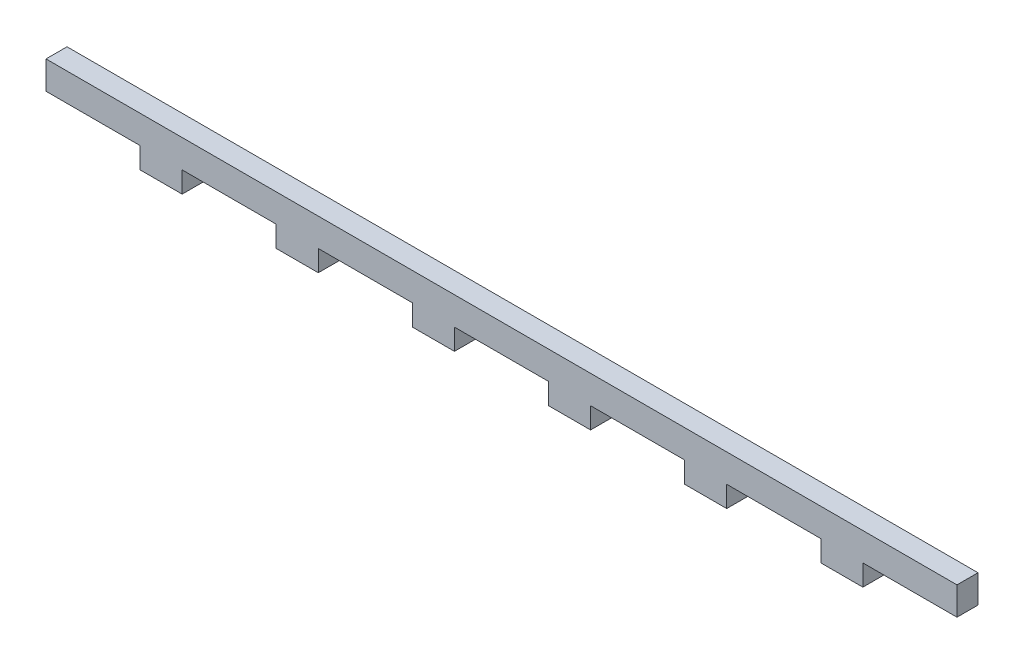
SolidWorks part; units mm, degrees
ref_plane "Front Plane" through (0, 0, 0) normal (0, 0, 1) x (1, 0, 0)
ref_plane "Top Plane" through (0, 0, 0) normal (0, 1, 0) x (1, 0, 0)
ref_plane "Right Plane" through (0, 0, 0) normal (1, 0, 0) x (0, 0, -1)
sketch "Sketch2" plane through (0, 0, 0) normal (0, 1, 0) x (1, 0, 0)
  line L0 (0, 0) -> (0, 6) construction
  dimension "D1" = 6
sketch "Sketch1" plane through (0, 0, 0) normal (0, 0, 1) x (1, 0, 0)
  line L1 (-130, -7) -> (130, -7)
  line L2 (-130, -7) -> (-130, 7)
  line L3 (-130, 7) -> (130, 7)
  line L4 (130, -7) -> (130, 7)
  line L5 (-130, -7) -> (130, 7) construction
  line L6 (-130, 7) -> (130, -7) construction
  point P0 (0, 0)
  dimension "D1" = 14
  dimension "D2" = 260
extrude "Boss-Extrude1" add sketch "Sketch1" against normal up to vertex (6 mm away) contours L2 L3 L4 L1 up to point (0, 0, -6)
sketch "Sketch3" plane through (0, 0, 0) normal (0, 0, 1) x (1, 0, 0)
  line L0 (-130, -7) -> (-130, 7) construction
  line L1 (-130, -1) -> (-103.1429, -1)
  line L2 (-130, -1) -> (-130, -7)
  line L3 (-130, -7) -> (-103.1429, -7)
  line L4 (-103.1429, -1) -> (-103.1429, -7)
  line L5 (-130, -7) -> (130, -7) construction
  line L6 (0, -1) -> (0, 0) construction
  line L7 (-103.1429, -1) -> (-91.1429, -1)
  line L8 (-103.1429, -1) -> (-103.1429, -7)
  line L9 (-103.1429, -7) -> (-91.1429, -7)
  line L10 (-91.1429, -1) -> (-91.1429, -7)
  line L11 (-91.1429, -1) -> (-64.2857, -1)
  line L12 (-91.1429, -1) -> (-91.1429, -7)
  line L13 (-91.1429, -7) -> (-64.2857, -7)
  line L14 (-64.2857, -1) -> (-64.2857, -7)
  line L15 (-64.2857, -1) -> (-52.2857, -1)
  line L16 (-64.2857, -1) -> (-64.2857, -7)
  line L17 (-64.2857, -7) -> (-52.2857, -7)
  line L18 (-52.2857, -1) -> (-52.2857, -7)
  line L19 (-52.2857, -1) -> (-25.4286, -1)
  line L20 (-52.2857, -1) -> (-52.2857, -7)
  line L21 (-52.2857, -7) -> (-25.4286, -7)
  line L22 (-25.4286, -1) -> (-25.4286, -7)
  line L23 (-25.4286, -1) -> (-13.4286, -1)
  line L24 (-25.4286, -1) -> (-25.4286, -7)
  line L25 (-25.4286, -7) -> (-13.4286, -7)
  line L26 (-13.4286, -1) -> (-13.4286, -7)
  line L27 (13.4286, -1) -> (-13.4286, -1)
  line L28 (0, -1) -> (0, -7)
  point P30 (0, -1)
  line M27 (-130, -7) -> (130, -7)
  line M30 (-130, 7) -> (-130, -7)
  dimension "D1" = 12
  dimension "D2" = 6
extrude "Cut-Extrude1" cut sketch "Sketch3" against normal through all contours L4 L1 M30 M27 | L14 L11 L10 M27 | L22 L19 L18 M27 | L28 L27 L26 M27
mirror "Mirror1" about plane through (0, 0, 0) normal (1, 0, 0) of "Cut-Extrude1"
equation "\"t_wood\"= 6' Thickness of the wood"
equation "\"t_glass\"= 2.5'Thickness of glass panels"
equation "\"w_glass\"= 248"
equation "\"h_glass\"= 167"
equation "\"h_food_internal\" = 60"
equation "\"entry_height\"= 20"
equation "\"entry diameter\"= 8"
equation "\"glass_bottom_overlap\"= 8"
equation "\"default_finger_size\"= 12"
equation "\"brood_depth\"= 42"
equation "\"outer_box_depth\" = \"brood_depth\" + ( 2 * \"t_glass\" ) + ( 2 * \"t_wood\" )"
equation "\"outer_box_width\"= \"w_glass\" + ( 2 * \"t_wood\" )"
equation "\"food_top_clearance\"= 10"
equation "\"outer_box_height\"= \"t_wood\" + \"h_glass\" + \"t_wood\" + \"h_food_internal\" + \"food_top_clearance\" + \"t_wood\""
equation "\"food_internal_depth\"= \"brood_depth\" + \"t_glass\" + \"t_glass\" - \"t_wood\" - \"t_wood\""
equation "\"food_channel_clearance_width\"= 14"
equation "\"bar_top_play\"= 4.5"
equation "\"bar_entry_angle\"= 10"
equation "\"bar_width\"= 20"
equation "\"entry_disk_play\"= 0.3"
equation "\"D1@Sketch2\"=\"t_wood\""
equation "\"D1@Sketch1\"=\"t_wood\"+\"glass_bottom_overlap\""
equation "\"D2@Sketch1\"=\"outer_box_width\""
equation "\"D1@Sketch3\"=\"default_finger_size\""
